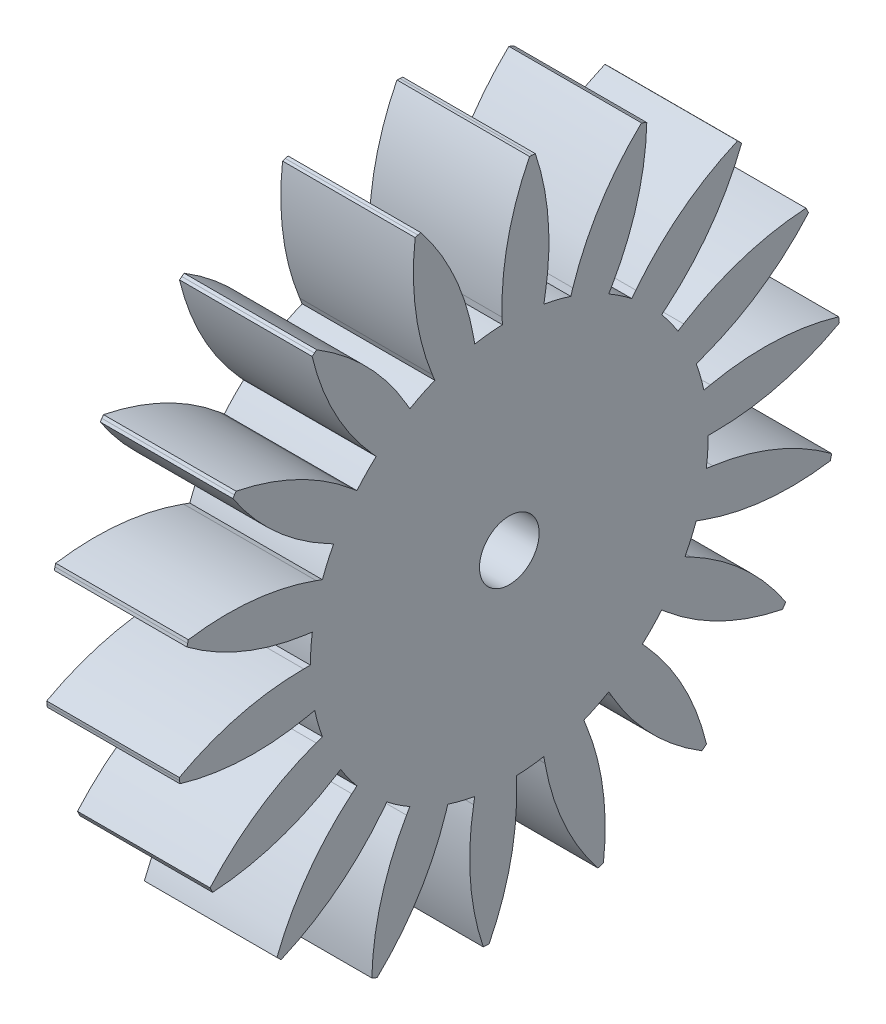
SolidWorks part; units mm, degrees
ref_plane "Front Plane" through (0, 0, 0) normal (0, 0, 1) x (1, 0, 0)
ref_plane "Top Plane" through (0, 0, 0) normal (0, 1, 0) x (1, 0, 0)
ref_plane "Right Plane" through (0, 0, 0) normal (1, 0, 0) x (0, 0, -1)
sketch "Sketch1" plane through (0, 0, 0) normal (1, 0, 0) x (0, 0, -1)
  line L0 (0, 0) -> (40, 0) construction
  line L1 (0, 0) -> (39.8158, 3.8338) construction
  line L2 (0, 0) -> (39.7809, 4.1811) construction
  line L3 (0, 0) -> (39.7429, 4.5281) construction
  line L4 (0, 0) -> (39.1259, 8.3165) construction
  line L5 (15, 0) -> (15.5, 0)
  line L6 (24.8849, 2.3961) -> (24.863, 2.6132)
  line L7 (24.8393, 2.8301) -> (24.863, 2.6132)
  line L8 (14.6722, 3.1187) -> (15.1613, 3.2226)
  line L9 (24.2037, -6.2595) -> (24.2574, -6.048)
  line L10 (24.3092, -5.8361) -> (24.2574, -6.048)
  line L11 (14.0954, -5.1303) -> (14.5652, -5.3013)
  line L12 (14.854, -2.0876) -> (15.3492, -2.1572)
  line L13 (20.6032, -14.1602) -> (20.7259, -13.9798)
  line L14 (20.8471, -13.7984) -> (20.7259, -13.9798)
  line L15 (11.4907, -9.6418) -> (11.8737, -9.9632)
  line L16 (13.2442, -7.0421) -> (13.6857, -7.2768)
  line L17 (14.5176, -20.3529) -> (14.6946, -20.2254)
  line L18 (14.8706, -20.0964) -> (14.6946, -20.2254)
  line L19 (7.5, -12.9904) -> (7.75, -13.4234)
  line L20 (10.037, -11.1472) -> (10.3715, -11.5187)
  line L21 (6.681, -24.0908) -> (6.8909, -24.0315)
  line L22 (7.1004, -23.9705) -> (6.8909, -24.0315)
  line L23 (2.6047, -14.7721) -> (2.6915, -15.2645)
  line L24 (5.6191, -13.9078) -> (5.8064, -14.3713)
  line L25 (-1.9615, -24.9229) -> (-1.7439, -24.9391)
  line L26 (-1.5262, -24.9534) -> (-1.7439, -24.9391)
  line L27 (-2.6047, -14.7721) -> (-2.6915, -15.2645)
  line L28 (0.5235, -14.9909) -> (0.5409, -15.4906)
  line L29 (-10.3673, -22.749) -> (-10.1684, -22.8386)
  line L30 (-9.9687, -22.9265) -> (-10.1684, -22.8386)
  line L31 (-7.5, -12.9904) -> (-7.75, -13.4234)
  line L32 (-4.6353, -14.2658) -> (-4.7898, -14.7414)
  line L33 (-17.5227, -17.8313) -> (-17.3665, -17.9835)
  line L34 (-17.2089, -18.1344) -> (-17.3665, -17.9835)
  line L35 (-11.4907, -9.6418) -> (-11.8737, -9.9632)
  line L36 (-9.2349, -11.8202) -> (-9.5428, -12.2142)
  line L37 (-22.5646, -10.7628) -> (-22.4699, -10.9593)
  line L38 (-22.3734, -11.1549) -> (-22.4699, -10.9593)
  line L39 (-14.0954, -5.1303) -> (-14.5652, -5.3013)
  line L40 (-12.7207, -7.9488) -> (-13.1447, -8.2137)
  line L41 (-24.8849, -2.3961) -> (-24.863, -2.6132)
  line L42 (-24.8393, -2.8301) -> (-24.863, -2.6132)
  line L43 (-15, 0) -> (-15.5, 0)
  line L44 (-14.6722, -3.1187) -> (-15.1613, -3.2226)
  line L45 (-24.2037, 6.2595) -> (-24.2574, 6.048)
  line L46 (-24.3092, 5.8361) -> (-24.2574, 6.048)
  line L47 (-14.0954, 5.1303) -> (-14.5652, 5.3013)
  line L48 (-14.854, 2.0876) -> (-15.3492, 2.1572)
  line L49 (-20.6032, 14.1602) -> (-20.7259, 13.9798)
  line L50 (-20.8471, 13.7984) -> (-20.7259, 13.9798)
  line L51 (-11.4907, 9.6418) -> (-11.8737, 9.9632)
  line L52 (-13.2442, 7.0421) -> (-13.6857, 7.2768)
  line L53 (-14.5176, 20.3529) -> (-14.6946, 20.2254)
  line L54 (-14.8706, 20.0964) -> (-14.6946, 20.2254)
  line L55 (-7.5, 12.9904) -> (-7.75, 13.4234)
  line L56 (-10.037, 11.1472) -> (-10.3715, 11.5187)
  line L57 (-6.681, 24.0908) -> (-6.8909, 24.0315)
  line L58 (-7.1004, 23.9705) -> (-6.8909, 24.0315)
  line L59 (-2.6047, 14.7721) -> (-2.6915, 15.2645)
  line L60 (-5.6191, 13.9078) -> (-5.8064, 14.3713)
  line L61 (1.9615, 24.9229) -> (1.7439, 24.9391)
  line L62 (1.5262, 24.9534) -> (1.7439, 24.9391)
  line L63 (2.6047, 14.7721) -> (2.6915, 15.2645)
  line L64 (-0.5235, 14.9909) -> (-0.5409, 15.4906)
  line L65 (10.3673, 22.749) -> (10.1684, 22.8386)
  line L66 (9.9687, 22.9265) -> (10.1684, 22.8386)
  line L67 (7.5, 12.9904) -> (7.75, 13.4234)
  line L68 (4.6353, 14.2658) -> (4.7898, 14.7414)
  line L69 (17.5227, 17.8313) -> (17.3665, 17.9835)
  line L70 (17.2089, 18.1344) -> (17.3665, 17.9835)
  line L71 (11.4907, 9.6418) -> (11.8737, 9.9632)
  line L72 (9.2349, 11.8202) -> (9.5428, 12.2142)
  line L73 (22.5646, 10.7628) -> (22.4699, 10.9593)
  line L74 (22.3734, 11.1549) -> (22.4699, 10.9593)
  line L75 (14.0954, 5.1303) -> (14.5652, 5.3013)
  line L76 (12.7207, 7.9488) -> (13.1447, 8.2137)
  circle A0 centre (0, 0) radius 2.25
  circle A1 centre (0, 0) radius 15
  circle A2 centre (0, 0) radius 25 construction
  arc A3 (15.5, 0) -> (24.8849, 2.3961) centre (15.5, 19.5769) ccw
  arc A4 (15.1613, 3.2226) -> (24.8393, 2.8301) centre (19.2315, -15.9264) cw
  arc A5 (15.3492, -2.1572) -> (24.3092, -5.8361) centre (12.6246, -21.5435) cw
  arc A6 (14.5652, -5.3013) -> (24.2037, -6.2595) centre (21.2609, 13.0949) ccw
  arc A7 (13.6857, -7.2768) -> (20.8471, -13.7984) centre (4.4949, -24.5622) cw
  arc A8 (11.8737, -9.9632) -> (20.6032, -14.1602) centre (24.4575, 5.0335) ccw
  arc A9 (10.3715, -11.5187) -> (14.8706, -20.0964) centre (-4.1769, -24.6182) cw
  arc A10 (7.75, -13.4234) -> (14.5176, -20.3529) centre (24.7041, -3.635) ccw
  arc A11 (5.8064, -14.3713) -> (7.1004, -23.9705) centre (-12.3449, -21.705) cw
  arc A12 (2.6915, -15.2645) -> (6.681, -24.0908) centre (21.971, -11.865) ccw
  arc A13 (0.5409, -15.4906) -> (-1.5262, -24.9534) centre (-19.024, -16.1738) cw
  arc A14 (-2.6915, -15.2645) -> (-1.9615, -24.9229) centre (16.5879, -18.664) ccw
  arc A15 (-4.7898, -14.7414) -> (-9.9687, -22.9265) centre (-23.4085, -8.6918) cw
  arc A16 (-7.75, -13.4234) -> (-10.3673, -22.749) centre (9.2041, -23.2118) ccw
  arc A17 (-9.5428, -12.2142) -> (-17.2089, -18.1344) centre (-24.9695, -0.1614) cw
  arc A18 (-11.8737, -9.9632) -> (-17.5227, -17.8313) centre (0.7101, -24.96) ccw
  arc A19 (-13.1447, -8.2137) -> (-22.3734, -11.1549) centre (-23.5189, 8.3884) cw
  arc A20 (-14.5652, -5.3013) -> (-22.5646, -10.7628) centre (-7.8696, -23.6975) ccw
  arc A21 (-15.1613, -3.2226) -> (-24.8393, -2.8301) centre (-19.2315, 15.9264) cw
  arc A22 (-15.5, 0) -> (-24.8849, -2.3961) centre (-15.5, -19.5769) ccw
  arc A23 (-15.3492, 2.1572) -> (-24.3092, 5.8361) centre (-12.6246, 21.5435) cw
  arc A24 (-14.5652, 5.3013) -> (-24.2037, 6.2595) centre (-21.2609, -13.0949) ccw
  arc A25 (-13.6857, 7.2768) -> (-20.8471, 13.7984) centre (-4.4949, 24.5622) cw
  arc A26 (-11.8737, 9.9632) -> (-20.6032, 14.1602) centre (-24.4575, -5.0335) ccw
  arc A27 (-10.3715, 11.5187) -> (-14.8706, 20.0964) centre (4.1769, 24.6182) cw
  arc A28 (-7.75, 13.4234) -> (-14.5176, 20.3529) centre (-24.7041, 3.635) ccw
  arc A29 (-5.8064, 14.3713) -> (-7.1004, 23.9705) centre (12.3449, 21.705) cw
  arc A30 (-2.6915, 15.2645) -> (-6.681, 24.0908) centre (-21.971, 11.865) ccw
  arc A31 (-0.5409, 15.4906) -> (1.5262, 24.9534) centre (19.024, 16.1738) cw
  arc A32 (2.6915, 15.2645) -> (1.9615, 24.9229) centre (-16.5879, 18.664) ccw
  arc A33 (4.7898, 14.7414) -> (9.9687, 22.9265) centre (23.4085, 8.6918) cw
  arc A34 (7.75, 13.4234) -> (10.3673, 22.749) centre (-9.2041, 23.2118) ccw
  arc A35 (9.5428, 12.2142) -> (17.2089, 18.1344) centre (24.9695, 0.1614) cw
  arc A36 (11.8737, 9.9632) -> (17.5227, 17.8313) centre (-0.7101, 24.96) ccw
  arc A37 (13.1447, 8.2137) -> (22.3734, 11.1549) centre (23.5189, -8.3884) cw
  arc A38 (14.5652, 5.3013) -> (22.5646, 10.7628) centre (7.8696, 23.6975) ccw
  point P10 (24.4537, 5.1978)
  point P11 (24.8393, 2.8301)
  point P12 (24.863, 2.6132)
  point P13 (24.8849, 2.3961)
  point P14 (15, 0)
  point P19 (24.874, 2.5047)
  point P20 (24.8512, 2.7216)
  point P182 (0, 0)
  dimension "D1" = 4.5
  dimension "D2" = 30
  dimension "D3" = 12
  dimension "D4" = 6
  dimension "D5" = 6.5
  dimension "D6" = 5.5
  dimension "D7" = 40
  dimension "D8" = 10
  dimension "D9" = 0.5
  dimension "D10" = 18
extrude "Boss-Extrude2" add sketch "Sketch1" along normal blind 10 contours L75 A38 L73 L74 A37 L76 A1 | L71 A36 L69 L70 A35 L72 A1 | L67 A34 L65 L66 A33 L68 A1 | L63 A32 L61 L62 A31 L64 A1 | L59 A30 L57 L58 A29 L60 A1 | L55 A28 L53 L54 A27 L56 A1 | L51 A26 L49 L50 A25 L52 A1 | L47 A24 L45 L46 A23 L48 A1 | L43 A22 L41 L42 A21 L44 A1 | L39 A20 L37 L38 A19 L40 A1 | L35 A18 L33 L34 A17 L36 A1 | L31 A16 L29 L30 A15 L32 A1 | L27 A14 L25 L26 A13 L28 A1 | L23 A12 L21 L22 A11 L24 A1 | L19 A10 L17 L18 A9 L20 A1 | L15 A8 L13 L14 A7 L16 A1 | L11 A6 L9 L10 A5 L12 A1 | A4 L8 A1 L5 A3 L6 L7 | A1 A0
equation "\"Gear_angle\"= 12"
equation "\"D3@Sketch1\"=\"Gear_angle\""
equation "\"D4@Sketch1\"=\"Gear_angle\"*0.5"
equation "\"D5@Sketch1\"=\"Gear_angle\"*0.5 +0.5"
equation "\"D6@Sketch1\"=\"Gear_angle\"*0.5 -0.5"
equation "\"Gear_diameter\"= 30mm"
equation "\"D2@Sketch1\"=\"Gear_diameter\""
equation "\"Gear_tooth_height\"= 2mm"
equation "\"gear_thickeness\"=10"
